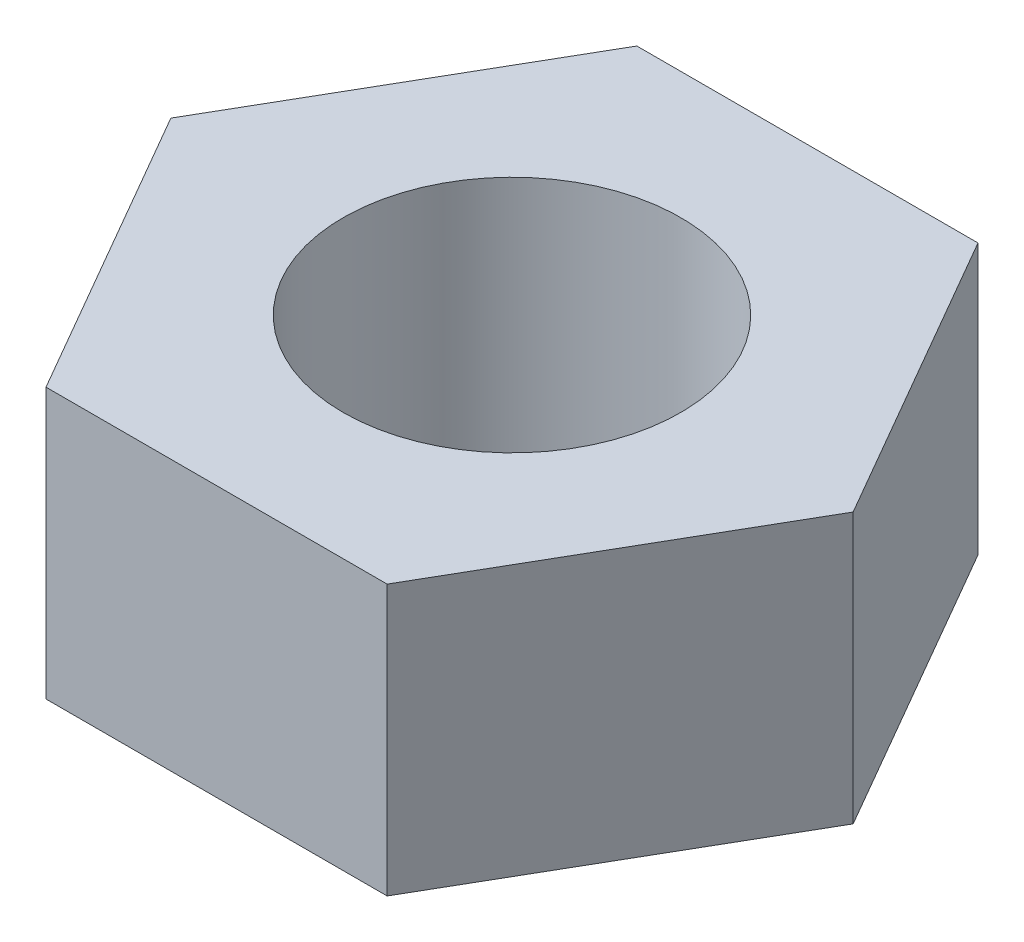
SolidWorks part; units mm, degrees
ref_plane "Front Plane" through (0, 0, 0) normal (0, 0, 1) x (1, 0, 0)
ref_plane "Top Plane" through (0, 0, 0) normal (0, 1, 0) x (1, 0, 0)
ref_plane "Right Plane" through (0, 0, 0) normal (1, 0, 0) x (0, 0, -1)
sketch "Sketch1" plane through (0, 0, 0) normal (0, 1, 0) x (1, 0, 0)
  line L1 (2.0207, -3.5) -> (4.0415, 0)
  line L2 (4.0415, 0) -> (2.0207, 3.5)
  line L3 (2.0207, 3.5) -> (-2.0207, 3.5)
  line L4 (-2.0207, 3.5) -> (-4.0415, 0)
  line L5 (-4.0415, 0) -> (-2.0207, -3.5)
  line L6 (-2.0207, -3.5) -> (2.0207, -3.5)
  circle A0 centre (0, 0) radius 3.5 construction
  circle A1 centre (0, 0) radius 2
  dimension "D2" = 4
  dimension "D1" = 7
extrude "Boss-Extrude1" add sketch "Sketch1" along normal blind 3.2
